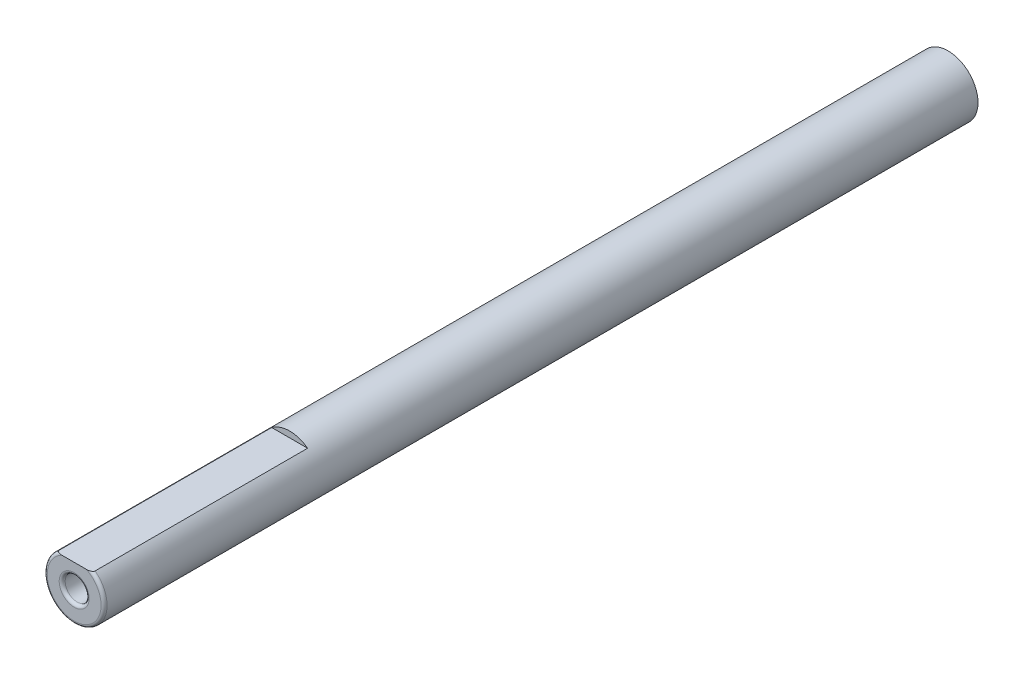
SolidWorks part; units mm, degrees
material "Acero aleado"
ref_plane "Plane1" through (0, 0, 0) normal (0, 0, 1) x (1, 0, 0)
ref_plane "Plane2" through (0, 0, 0) normal (0, 1, 0) x (1, 0, 0)
ref_plane "Plane3" through (0, 0, 0) normal (1, 0, 0) x (0, 0, -1)
sketch "Sketch1" plane through (0, 0, 0) normal (0, 0, 1) x (1, 0, 0)
  circle A0 centre (0, 0) radius 2.5
  dimension "D1" = 5
extrude "Extrude1" add sketch "Sketch1" along normal blind 73
sketch "Sketch2" plane through (0, 0, 73) normal (0, 0, 1) x (1, 0, 0)
  circle A0 centre (0, 0) radius 1
  dimension "D1" = 2
extrude "ICE1" cut sketch "Sketch2" against normal blind 10
fillet "Fillet1" radius 0.25 2 edges at (2.5, 0, 73) (1, 0, 73)
sketch "Sketch4" plane through (0, 0, 73) normal (0, 0, 1) x (1, 0, 0)
  line L0 (-1.5, 2) -> (1.5, 2)
  circle A0 centre (0, 0) radius 2.5 construction
  arc A1 (1.5, 2) -> (-1.5, 2) centre (0, 0) ccw
  point P4 (0, -2.5)
  dimension "D1" = 4.5
extrude "Cut-Extrude1" cut sketch "Sketch4" against normal blind 18
